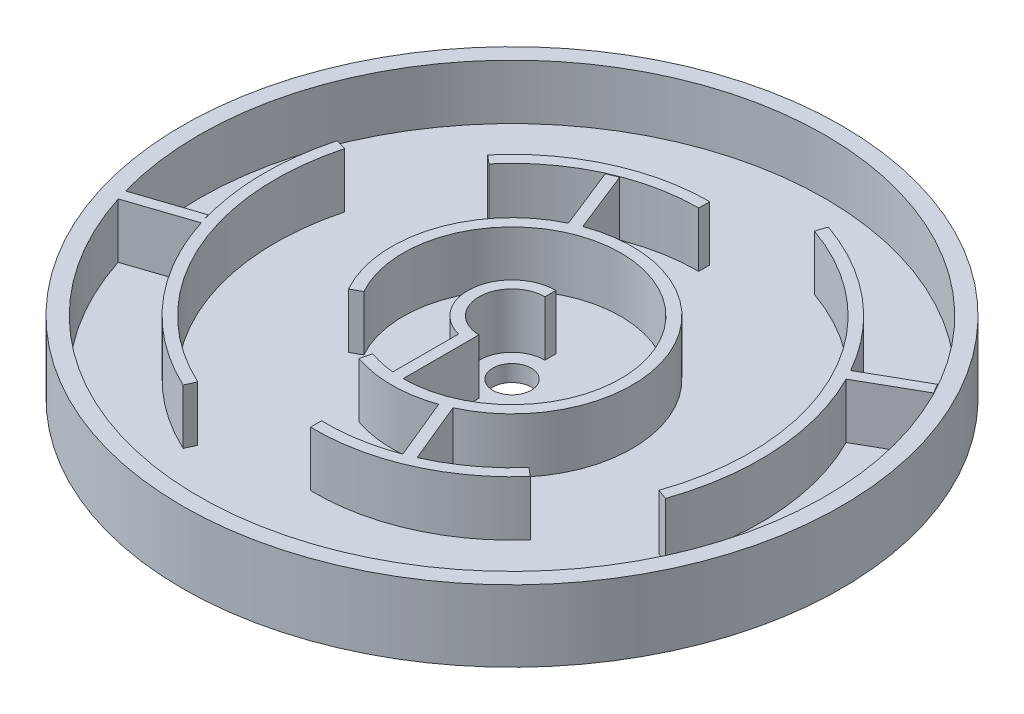
SolidWorks part; units mm, degrees
ref_plane "Front Plane" through (0, 0, 0) normal (0, 0, 1) x (1, 0, 0)
ref_plane "Top Plane" through (0, 0, 0) normal (0, 1, 0) x (1, 0, 0)
ref_plane "Right Plane" through (0, 0, 0) normal (1, 0, 0) x (0, 0, -1)
sketch "Sketch1" plane through (0, 0, 0) normal (0, 1, 0) x (1, 0, 0)
  circle A0 centre (0, 0) radius 76.2
extrude "Boss-Extrude1" add sketch "Sketch1" along normal blind 3.81
sketch "Sketch2" plane through (0, 3.81, 0) normal (0, 1, 0) x (1, 0, 0)
  circle A0 centre (0, 0) radius 72.39
  circle A1 centre (0, 0) radius 76.2
extrude "Boss-Extrude2" add sketch "Sketch2" along normal blind 12.7
sketch "Sketch3" plane through (0, 3.81, 0) normal (0, 1, 0) x (1, 0, 0)
  circle A0 centre (0, 0) radius 4.445
extrude "Cut-Extrude1" cut sketch "Sketch3" against normal through all
sketch "Sketch4" plane through (0, 3.81, 0) normal (0, 1, 0) x (1, 0, 0)
  line L0 (0, 7.62) -> (0, 10.16)
  line L1 (0, -7.62) -> (0, -10.16)
  arc A0 (0, 7.62) -> (0, -7.62) centre (0, 0) ccw
  arc A1 (0, 10.16) -> (0, -10.16) centre (0, 0) ccw
  dimension "D1" = 7.62
extrude "Boss-Extrude3" add sketch "Sketch4" along normal blind 12.7
sketch "Sketch5" plane through (0, 3.81, 0) normal (0, 1, 0) x (1, 0, 0)
  line L0 (0, -10.16) -> (0, -25.1767)
  line L1 (0, -25.1767) -> (-2.54, -25.1767)
  line L2 (-2.54, -25.1767) -> (-2.5201, -9.8425)
  line L3 (-2.5201, -9.8425) -> (0, -10.16)
  arc A0 (0, 10.16) -> (0, -10.16) centre (0, 0) ccw construction
  dimension "D1" = 2.54
  dimension "D2" = 2.54
extrude "Boss-Extrude4" add sketch "Sketch5" along normal blind 12.7
sketch "Sketch6" plane through (0, 3.81, 0) normal (0, 1, 0) x (1, 0, 0)
  line L0 (-21.9835, -12.2652) -> (-24.2679, -13.5397)
  line L1 (-8.4722, -23.7051) -> (-9.1352, -26.2451)
  arc A0 (-8.4722, -23.7051) -> (-21.9835, -12.2652) centre (0, 0) ccw
  arc A1 (-24.2679, -13.5397) -> (-9.1352, -26.2451) centre (0, 0) cw
  dimension "D1" = 2.54
extrude "Boss-Extrude5" add sketch "Sketch6" along normal blind 12.7
sketch "Sketch7" plane through (0, 3.81, 0) normal (0, 1, 0) x (1, 0, 0)
  line L0 (9.2475, -26.2057) -> (15.1285, -40.4543)
  line L1 (15.1285, -40.4543) -> (17.4764, -39.4853)
  line L2 (17.4764, -39.4853) -> (11.6017, -25.2519)
  line L3 (11.6017, -25.2519) -> (9.2475, -26.2057)
  line L4 (26.0169, -34.4621) -> (27.5586, -36.5047)
  line L5 (5.2746, -42.8566) -> (5.5872, -45.3966)
  arc A0 (-9.1352, -26.2451) -> (-24.2679, -13.5397) centre (0, 0) ccw construction
  arc A1 (5.2746, -42.8566) -> (26.0169, -34.4621) centre (0, 0) ccw
  arc A2 (5.5872, -45.3966) -> (27.5586, -36.5047) centre (0, 0) ccw
  dimension "D3" = 43.18
  dimension "D1" = 2.54
  dimension "D2" = 15.4146
  dimension "D4" = 22.3766
  dimension "D5" = 30.034
  dimension "D7" = 2.54
extrude "Boss-Extrude8" add sketch "Sketch7" along normal blind 12.7 contours L2 L3 L0 L1
sketch "Sketch8" plane through (0, 3.81, 0) normal (0, 1, 0) x (1, 0, 0)
  line L0 (-0.9837, -43.0491) -> (-0.9837, -45.5891)
  line L1 (32.3452, -28.425) -> (34.2909, -30.0577)
  arc A0 (-0.9837, -43.0491) -> (32.3452, -28.425) centre (0, 0) ccw
  arc A1 (-0.9837, -45.5891) -> (34.2909, -30.0577) centre (0, 0) ccw
  dimension "D1" = 2.54
  dimension "D2" = 50
extrude "Boss-Extrude9" add sketch "Sketch8" along normal blind 12.7
sketch "Sketch9" plane through (0, 3.81, 0) normal (0, 1, 0) x (1, 0, 0)
  line L0 (-9.6845, 26.0474) -> (-12.0223, 25.0543)
  line L1 (-9.6845, 26.0474) -> (-15.3085, 40.2117)
  line L2 (-12.0223, 25.0543) -> (-17.6464, 39.2186)
  line L3 (-17.6464, 39.2186) -> (-15.3085, 40.2117)
  line L4 (1.8893, 43.1378) -> (1.8893, 45.6778)
  line L5 (-33.7768, 30.8084) -> (-31.7159, 29.3008)
  arc A0 (11.6017, -25.2519) -> (-24.2679, -13.5397) centre (0, 0) ccw construction
  arc A1 (1.8893, 43.1378) -> (-31.7159, 29.3008) centre (0, 0) ccw
  arc A2 (1.8893, 45.6778) -> (-33.7768, 30.8084) centre (0, 0) ccw
  dimension "D1" = 2.54
  dimension "D2" = 130
extrude "Boss-Extrude10" add sketch "Sketch9" along normal blind 12.7 contours L1 L3 L2 L0
sketch "Sketch10" plane through (0, 3.81, 0) normal (0, 1, 0) x (1, 0, 0)
  line L0 (0, 43.18) -> (0, 45.72)
  line L1 (-33.0778, 27.7556) -> (-35.0236, 29.3882)
  arc A0 (0, 43.18) -> (-33.0778, 27.7556) centre (0, 0) ccw
  arc A1 (0, 45.72) -> (-35.0236, 29.3882) centre (0, 0) ccw
  dimension "D1" = 130
extrude "Boss-Extrude11" add sketch "Sketch10" along normal blind 12.7
sketch "Sketch15" plane through (0, 16.51, 0) normal (0, 1, 0) x (1, 0, 0)
  line L0 (18.8132, 54.3318) -> (17.9821, 51.9316)
  line L1 (51.9316, -17.9821) -> (54.3318, -18.8132)
  arc A0 (18.8132, 54.3318) -> (54.3318, -18.8132) centre (0, 0) cw
  arc A1 (17.9821, 51.9316) -> (51.9316, -17.9821) centre (0, 0) cw
  dimension "D2" = 57.4968
  dimension "D1" = 2.54
  dimension "D3" = 90
extrude "Boss-Extrude19" add sketch "Sketch15" against normal blind 12.7
sketch "Sketch16" plane through (0, 3.81, 0) normal (0, 1, 0) x (1, 0, 0)
  line L0 (62.9237, 35.48) -> (64.1797, 33.2722)
  line L1 (64.1797, 33.2722) -> (50.9333, 25.7363)
  line L2 (50.9333, 25.7363) -> (49.6773, 27.944)
  line L3 (62.9237, 35.48) -> (49.6773, 27.944)
  dimension "D1" = 2.54
  dimension "D2" = 2.54
  dimension "D3" = 15.24
extrude "Boss-Extrude20" add sketch "Sketch16" along normal blind 12.7
sketch "Sketch17" plane through (0, 3.81, 0) normal (0, 1, 0) x (1, 0, 0)
  line L0 (-69.7854, -19.726) -> (-68.9824, -22.1357)
  line L1 (-68.9824, -22.1357) -> (-54.5241, -17.3177)
  line L2 (-54.5241, -17.3177) -> (-55.3271, -14.9079)
  line L3 (-55.3271, -14.9079) -> (-69.7854, -19.726)
extrude "Boss-Extrude21" add sketch "Sketch17" along normal blind 12.7
sketch "Sketch18" plane through (0, 3.81, 0) normal (0, 1, 0) x (1, 0, 0)
  line L0 (-24.165, -51.8735) -> (-23.0924, -49.5711)
  line L1 (-55.2816, 14.7901) -> (-52.8275, 14.1352)
  arc A0 (-55.2816, 14.7901) -> (-24.165, -51.8735) centre (0, 0) ccw
  arc A1 (-23.0924, -49.5711) -> (-52.8275, 14.1352) centre (0, 0) cw
  dimension "D1" = 57.2259
  dimension "D2" = 80
  dimension "D3" = 2.54
extrude "Boss-Extrude22" add sketch "Sketch18" along normal blind 12.7
